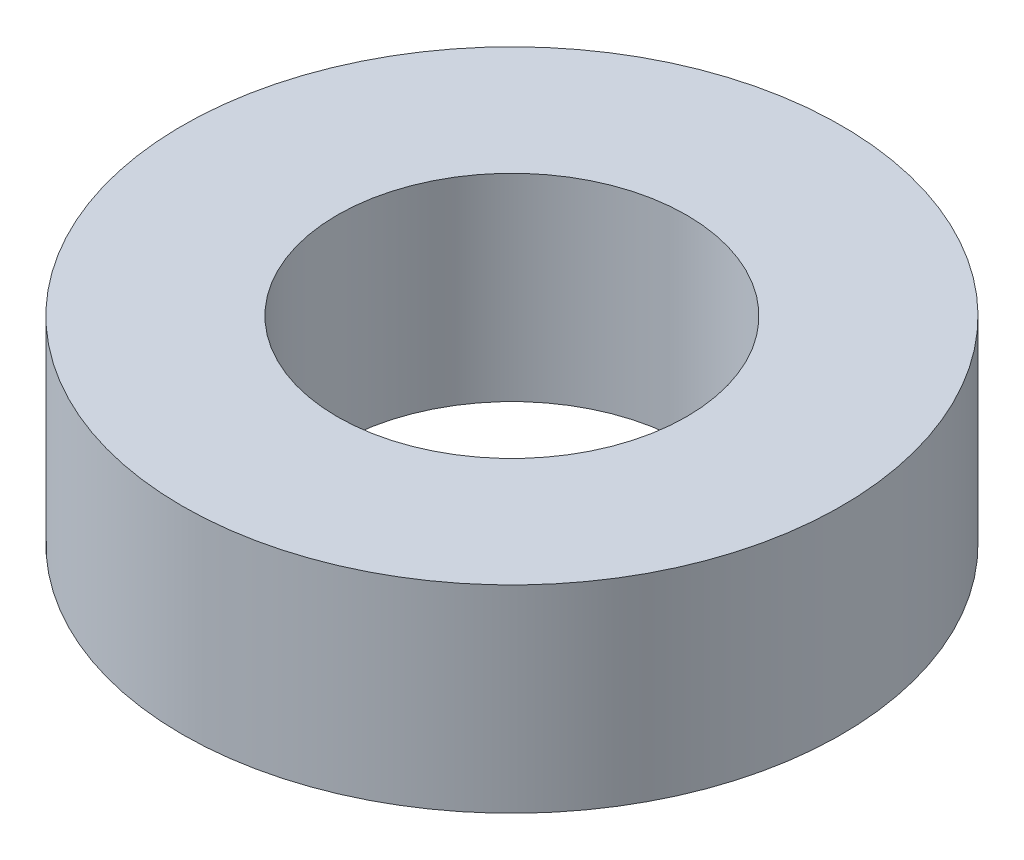
SolidWorks part; units mm, degrees
ref_plane "Front Plane" through (0, 0, 0) normal (0, 0, 1) x (1, 0, 0)
ref_plane "Top Plane" through (0, 0, 0) normal (0, 1, 0) x (1, 0, 0)
ref_plane "Right Plane" through (0, 0, 0) normal (1, 0, 0) x (0, 0, -1)
sketch "Sketch1" plane through (0, 0, 0) normal (0, 1, 0) x (1, 0, 0)
  circle A0 centre (0, 0) radius 5
  circle A1 centre (0, 0) radius 2.65
  dimension "D1" = 10
  dimension "D2" = 5.3
extrude "Boss-Extrude1" add sketch "Sketch1" along normal blind 3
